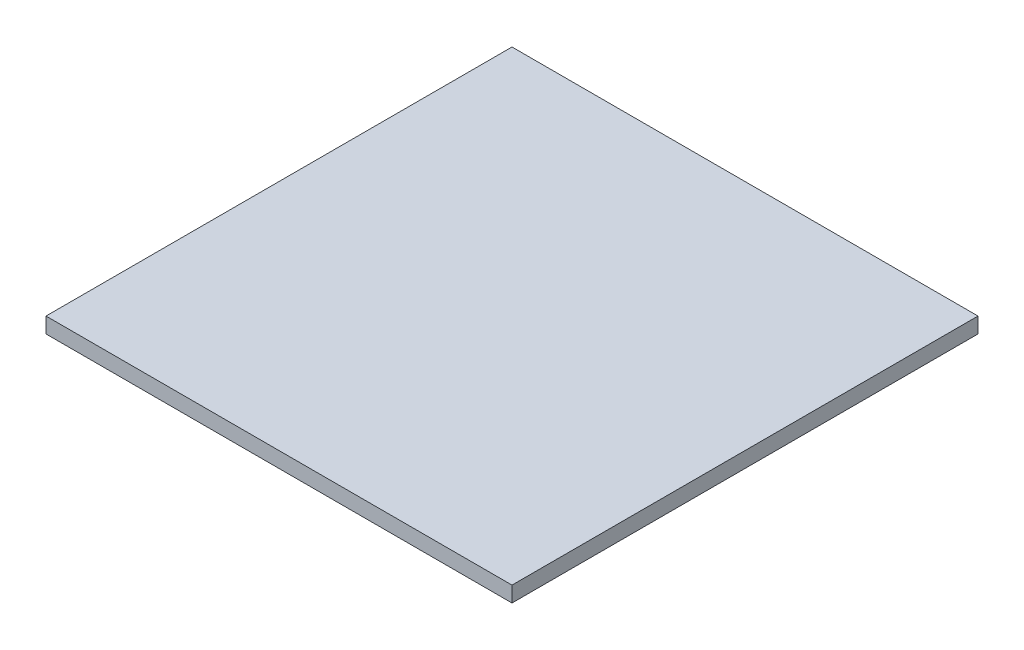
SolidWorks part; units mm, degrees
ref_plane "Front Plane" through (0, 0, 0) normal (0, 0, 1) x (1, 0, 0)
ref_plane "Top Plane" through (0, 0, 0) normal (0, 1, 0) x (1, 0, 0)
ref_plane "Right Plane" through (0, 0, 0) normal (1, 0, 0) x (0, 0, -1)
sketch "Sketch1" plane through (0, 0, 0) normal (0, 1, 0) x (1, 0, 0)
  line L1 (-150, 150) -> (150, 150)
  line L2 (-150, 150) -> (-150, -150)
  line L3 (-150, -150) -> (150, -150)
  line L4 (150, 150) -> (150, -150)
  line L5 (-150, 150) -> (150, -150) construction
  line L6 (-150, -150) -> (150, 150) construction
  point P0 (0, 0)
  dimension "D1" = 300
extrude "Boss-Extrude1" add sketch "Sketch1" against normal mid plane 10
